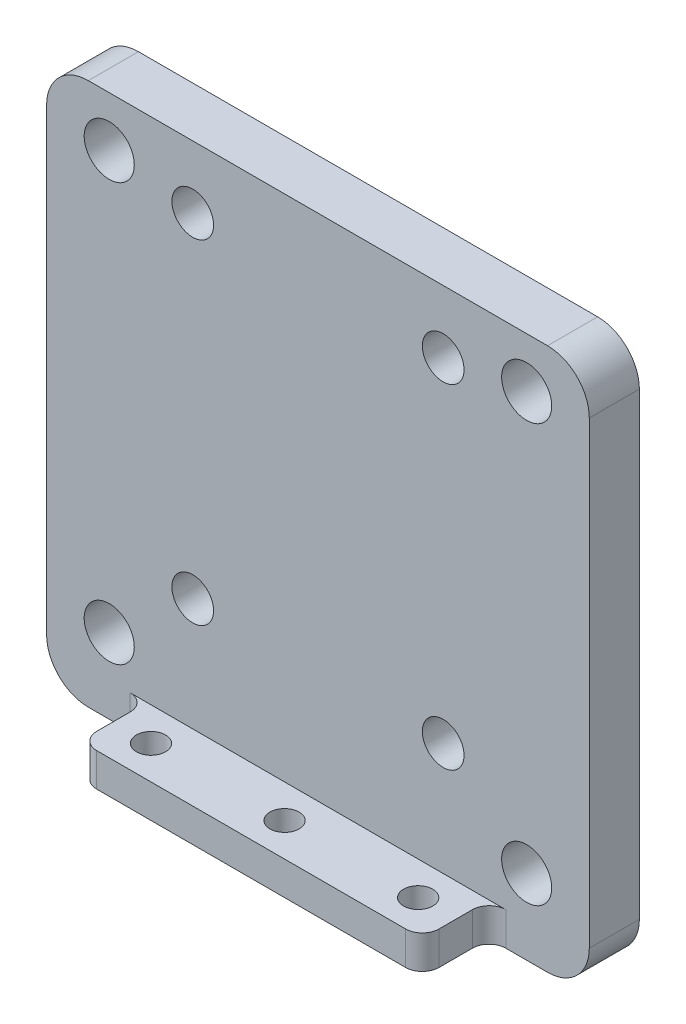
SolidWorks part; units mm, degrees
ref_plane "Front Plane" through (0, 0, 0) normal (0, 0, 1) x (1, 0, 0)
ref_plane "Top Plane" through (0, 0, 0) normal (0, 1, 0) x (1, 0, 0)
ref_plane "Right Plane" through (0, 0, 0) normal (1, 0, 0) x (0, 0, -1)
sketch "Sketch1" plane through (0, 0, 0) normal (0, 0, 1) x (1, 0, 0)
  line L0 (0, 1.5) -> (0, 0) construction
  line L1 (-32.5, 32.5) -> (32.5, 32.5)
  line L2 (-32.5, 32.5) -> (-32.5, -32.5)
  line L3 (-32.5, -32.5) -> (32.5, -32.5)
  line L4 (32.5, 32.5) -> (32.5, -32.5)
  line L5 (-32.5, 32.5) -> (32.5, -32.5) construction
  line L6 (-32.5, -32.5) -> (32.5, 32.5) construction
  line L7 (25, -23.5) -> (-25, -23.5) construction
  line L8 (25, -23.5) -> (25, 26.5) construction
  line L9 (25, 26.5) -> (-25, 26.5) construction
  line L10 (-25, -23.5) -> (-25, 26.5) construction
  line L11 (25, -23.5) -> (-25, 26.5) construction
  line L12 (25, 26.5) -> (-25, -23.5) construction
  circle A0 centre (25, 26.5) radius 3
  circle A1 centre (25, -23.5) radius 3
  circle A2 centre (-25, -23.5) radius 3
  circle A3 centre (-25, 26.5) radius 3
  point P0 (0, 0)
  point P6 (0, 1.5)
  dimension "D3" = 6
  dimension "D1" = 65
  dimension "D2" = 65
  dimension "D4" = 50
  dimension "D5" = 6
extrude "Boss-Extrude1" add sketch "Sketch1" along normal blind 6
fillet "Fillet1" radius 5 4 edges at (32.5, -32.5, 3) (-32.5, -32.5, 3) (32.5, 32.5, 3) (-32.5, 32.5, 3)
sketch "Sketch2" plane through (0, 0, 6) normal (0, 0, 1) x (1, 0, 0)
  line L0 (-27.5, -32.5) -> (27.5, -32.5) construction
  line L1 (-20.5, -32.5) -> (20.5, -32.5)
  line L2 (-20.5, -32.5) -> (-20.5, -28.5)
  line L3 (-20.5, -28.5) -> (20.5, -28.5)
  line L4 (20.5, -32.5) -> (20.5, -28.5)
  line L5 (0, 0) -> (0, -28.5) construction
  dimension "D1" = 41
  dimension "D2" = 4
extrude "Boss-Extrude2" add sketch "Sketch2" along normal blind 8
fillet "Fillet2" radius 2 4 edges at (20.5, -30.5, 6) (20.5, -30.5, 14) (-20.5, -30.5, 14) (-20.5, -30.5, 6)
sketch "Sketch3" plane through (0, 0, 0) normal (0, 0, -1) x (-1, 0, 0)
  line L0 (-15, 25) -> (15, -15) construction
  line L1 (-15, 25) -> (15, 25) construction
  line L2 (-15, 25) -> (-15, -15) construction
  line L3 (-15, -15) -> (15, -15) construction
  line L4 (15, 25) -> (15, -15) construction
  line L5 (0, 0) -> (0, 5) construction
  circle A0 centre (-15, 25) radius 2.5
  circle A1 centre (15, 25) radius 2.5
  circle A2 centre (-15, -15) radius 2.5
  circle A3 centre (15, -15) radius 2.5
  dimension "D1" = 5
  dimension "D2" = 40
  dimension "D3" = 30
  dimension "D4" = 5
extrude "Cut-Extrude1" cut sketch "Sketch3" against normal through all
sketch "草图1" plane through (0, -32.5, 0) normal (0, -1, 0) x (1, 0, 0)
  line L0 (-16, 10) -> (0, 10) construction
  line L1 (0, 10) -> (16, 10) construction
  line L2 (-18.5, 14) -> (18.5, 14) construction
  circle A0 centre (-16, 10) radius 1.75
  circle A1 centre (0, 10) radius 1.75
  circle A2 centre (16, 10) radius 1.75
  dimension "D2" = 3.5
  dimension "D1" = 16
  dimension "D3" = 4
extrude "切除-拉伸1" cut sketch "草图1" against normal through all
